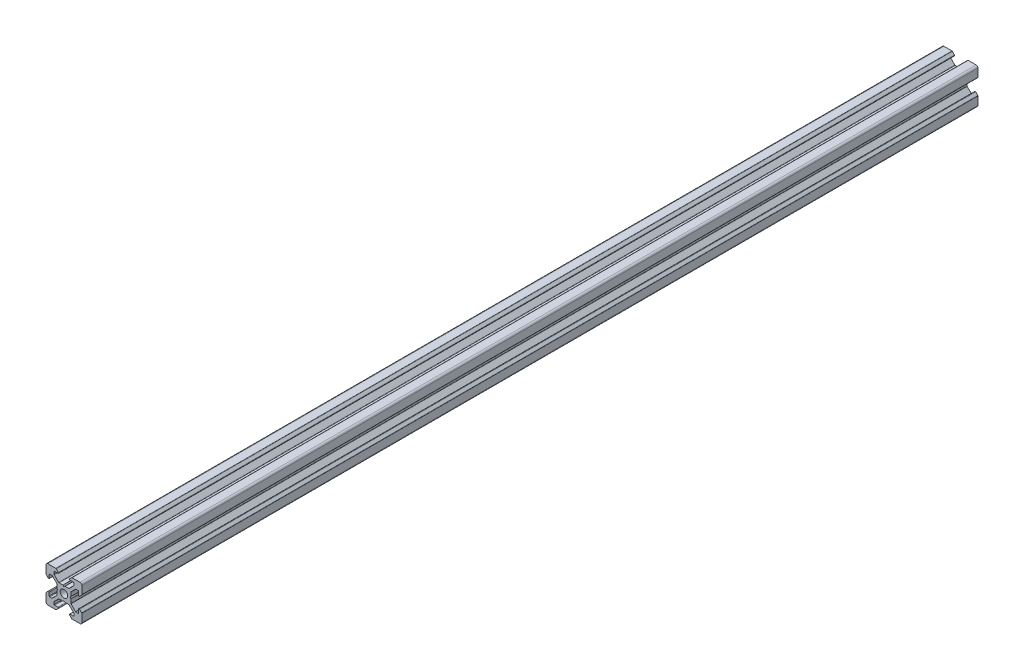
SolidWorks part; units mm, degrees
material "1060 СплавА"
ref_plane "Спереди" through (0, 0, 0) normal (0, 0, 1) x (1, 0, 0)
ref_plane "Сверху" through (0, 0, 0) normal (0, 1, 0) x (1, 0, 0)
ref_plane "Справа" through (0, 0, 0) normal (1, 0, 0) x (0, 0, -1)
sketch "Эскиз1" plane through (0, 0, 0) normal (0, 0, 1) x (1, 0, 0)
  line L0 (0, -12.9654) -> (0, 12.9654) construction
  line L1 (-12.9654, 0) -> (12.9654, 0) construction
  line L2 (0, 0) -> (-18.3359, 18.3359) construction
  line L3 (-10, 10) -> (-4.4, 10)
  line L4 (-4.4, 10) -> (-2.6, 8.2)
  line L5 (-2.6, 8.2) -> (-5.4993, 8.2)
  line L6 (-5.4993, 8.2) -> (-5.4993, 6.56)
  line L7 (-5.4993, 6.56) -> (-2.84, 3.9007)
  line L8 (-2.84, 3.9007) -> (-0.5, 3.9007)
  line L9 (-0.5, 3.9007) -> (0, 3.4007)
  line L10 (-3.9007, 0.5) -> (-3.4007, 0)
  line L11 (-3.9007, 2.84) -> (-3.9007, 0.5)
  line L12 (-6.56, 5.4993) -> (-3.9007, 2.84)
  line L13 (-8.2, 5.4993) -> (-6.56, 5.4993)
  line L14 (-8.2, 2.6) -> (-8.2, 5.4993)
  line L15 (-10, 4.4) -> (-8.2, 2.6)
  line L16 (-10, 10) -> (-10, 4.4)
  line L17 (10, 10) -> (10, 4.4)
  line L18 (10, 4.4) -> (8.2, 2.6)
  line L19 (8.2, 2.6) -> (8.2, 5.4993)
  line L20 (8.2, 5.4993) -> (6.56, 5.4993)
  line L21 (6.56, 5.4993) -> (3.9007, 2.84)
  line L22 (3.9007, 2.84) -> (3.9007, 0.5)
  line L23 (3.9007, 0.5) -> (3.4007, 0)
  line L24 (0.5, 3.9007) -> (0, 3.4007)
  line L25 (2.84, 3.9007) -> (0.5, 3.9007)
  line L26 (5.4993, 6.56) -> (2.84, 3.9007)
  line L27 (5.4993, 8.2) -> (5.4993, 6.56)
  line L28 (2.6, 8.2) -> (5.4993, 8.2)
  line L29 (4.4, 10) -> (2.6, 8.2)
  line L30 (10, 10) -> (4.4, 10)
  line L31 (3.9007, -0.5) -> (3.4007, 0)
  line L32 (-3.9007, -0.5) -> (-3.4007, 0)
  line L33 (10, -10) -> (4.4, -10)
  line L34 (4.4, -10) -> (2.6, -8.2)
  line L35 (2.6, -8.2) -> (5.4993, -8.2)
  line L36 (5.4993, -8.2) -> (5.4993, -6.56)
  line L37 (5.4993, -6.56) -> (2.84, -3.9007)
  line L38 (2.84, -3.9007) -> (0.5, -3.9007)
  line L39 (0.5, -3.9007) -> (0, -3.4007)
  line L40 (3.9007, -2.84) -> (3.9007, -0.5)
  line L41 (6.56, -5.4993) -> (3.9007, -2.84)
  line L42 (8.2, -5.4993) -> (6.56, -5.4993)
  line L43 (8.2, -2.6) -> (8.2, -5.4993)
  line L44 (10, -4.4) -> (8.2, -2.6)
  line L45 (10, -10) -> (10, -4.4)
  line L46 (-10, -10) -> (-10, -4.4)
  line L47 (-10, -4.4) -> (-8.2, -2.6)
  line L48 (-8.2, -2.6) -> (-8.2, -5.4993)
  line L49 (-8.2, -5.4993) -> (-6.56, -5.4993)
  line L50 (-6.56, -5.4993) -> (-3.9007, -2.84)
  line L51 (-3.9007, -2.84) -> (-3.9007, -0.5)
  line L52 (-0.5, -3.9007) -> (0, -3.4007)
  line L53 (-2.84, -3.9007) -> (-0.5, -3.9007)
  line L54 (-5.4993, -6.56) -> (-2.84, -3.9007)
  line L55 (-5.4993, -8.2) -> (-5.4993, -6.56)
  line L56 (-2.6, -8.2) -> (-5.4993, -8.2)
  line L57 (-4.4, -10) -> (-2.6, -8.2)
  line L58 (-10, -10) -> (-4.4, -10)
  circle A0 centre (0, 0) radius 2.1
  dimension "D5" = 2.6
  dimension "D10" = 4.2
  dimension "D2" = 10
  dimension "D3" = 1.64
  dimension "D4" = 1.5
  dimension "D6" = 1.8
  dimension "D7" = 2.84
  dimension "D8" = 0.5
  dimension "D9" = 45
extrude "Бобышка-Вытянуть1" add sketch "Эскиз1" along normal blind 500
fillet "Скругление1" radius 1 4 edges at (-10, -10, 250) (10, -10, 250) (10, 10, 250) (-10, 10, 250)
fillet "Скругление2" radius 0.3 47 edges at (10, 4.4, 250) (8.2, 2.6, 250) (8.2, 5.4993, 250) (6.56, 5.4993, 250) (3.9007, 2.84, 250) (3.9007, 0.5, 250) (3.9007, -0.5, 250) (3.9007, -2.84, 250) (6.56, -5.4993, 250) (10, -4.4, 250) (8.2, -5.4993, 250) (8.2, -2.6, 250) (4.4, -10, 250) (2.6, -8.2, 250) (5.4993, -8.2, 250) (5.4993, -6.56, 250) (2.84, -3.9007, 250) (0.5, -3.9007, 250) (-0.5, -3.9007, 250) (-2.84, -3.9007, 250) (-5.4993, -6.56, 250) (-5.4993, -8.2, 250) (-2.6, -8.2, 250) (-4.4, -10, 250) (-10, -4.4, 250) (-8.2, -2.6, 250) (-8.2, -5.4993, 250) (-6.56, -5.4993, 250) (-3.9007, -2.84, 250) (-3.9007, -0.5, 250) (-3.9007, 0.5, 250) (-3.9007, 2.84, 250) (-6.56, 5.4993, 250) (-8.2, 5.4993, 250) (-8.2, 2.6, 250) (-4.4, 10, 250) (-2.6, 8.2, 250) (-5.4993, 8.2, 250) (-5.4993, 6.56, 250) (-2.84, 3.9007, 250) (-0.5, 3.9007, 250) (0.5, 3.9007, 250) (2.84, 3.9007, 250) (5.4993, 6.56, 250) (5.4993, 8.2, 250) (2.6, 8.2, 250) (4.4, 10, 250)
